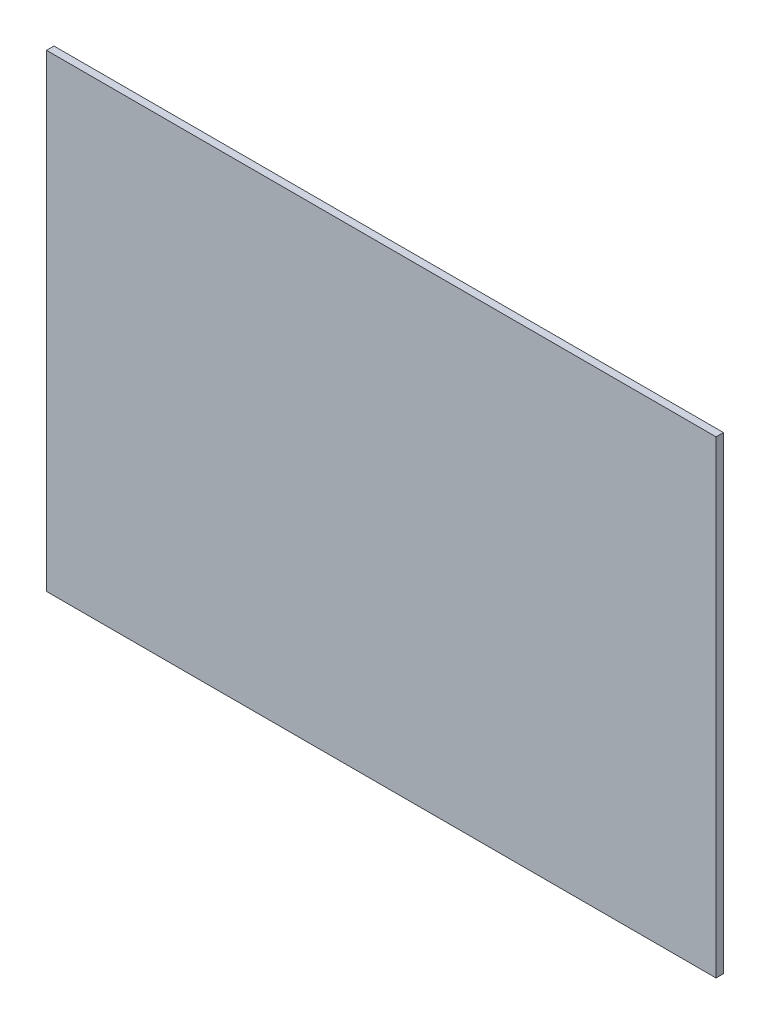
SolidWorks part; units mm, degrees
ref_plane "Plan de face" through (0, 0, 0) normal (0, 0, 1) x (1, 0, 0)
ref_plane "Plan de dessus" through (0, 0, 0) normal (0, 1, 0) x (1, 0, 0)
ref_plane "Plan de droite" through (0, 0, 0) normal (1, 0, 0) x (0, 0, -1)
sketch "Esquisse1" plane through (0, 0, 0) normal (0, 0, 1) x (1, 0, 0)
  line L1 (0, 0) -> (180, 0)
  line L2 (0, 0) -> (0, 126)
  line L3 (0, 126) -> (180, 126)
  line L4 (180, 0) -> (180, 126)
  dimension "D1" = 126
  dimension "D2" = 180
extrude "Boss.-Extru.1" add sketch "Esquisse1" along normal blind 2
